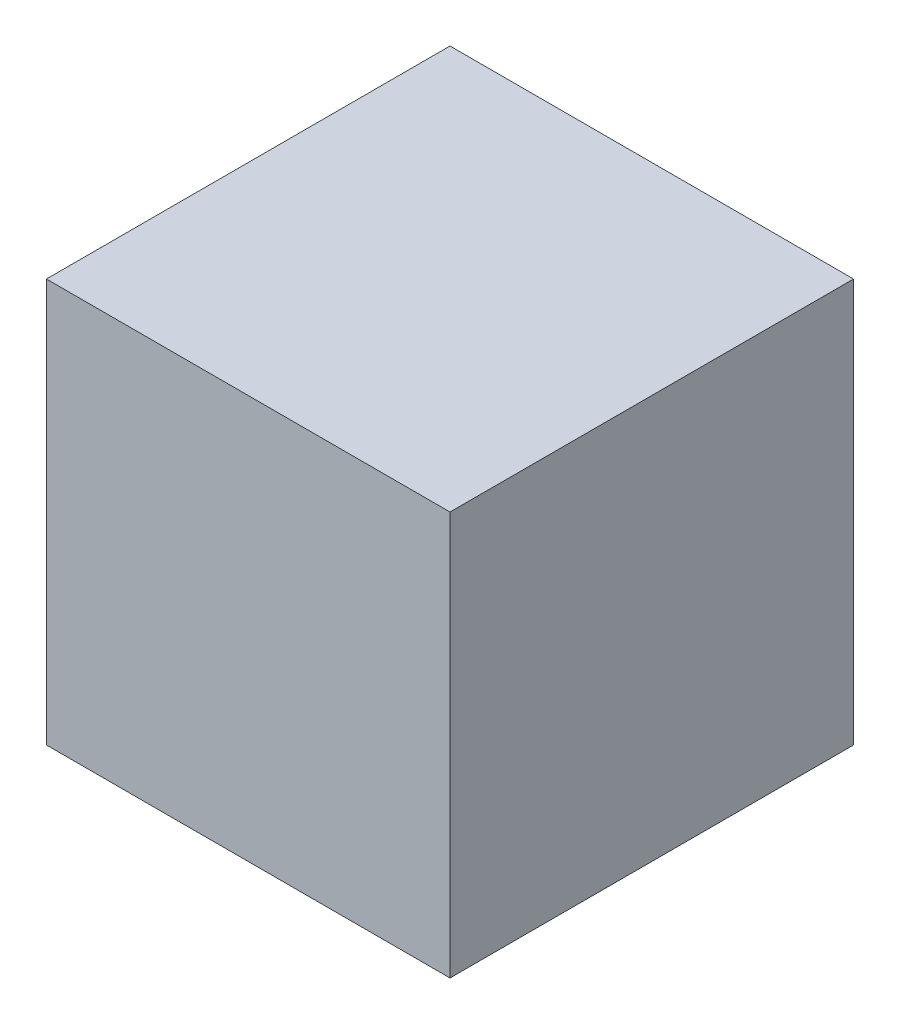
SolidWorks part; units mm, degrees
ref_plane "Plano frontal" through (0, 0, 0) normal (0, 0, 1) x (1, 0, 0)
ref_plane "Plano superior" through (0, 0, 0) normal (0, 1, 0) x (1, 0, 0)
ref_plane "Plano direito" through (0, 0, 0) normal (1, 0, 0) x (0, 0, -1)
sketch "Esboço1" plane through (0, 0, 0) normal (0, 1, 0) x (1, 0, 0)
  line L1 (5, -5) -> (-5, -5)
  line L2 (5, -5) -> (5, 5)
  line L3 (5, 5) -> (-5, 5)
  line L4 (-5, -5) -> (-5, 5)
  line L5 (5, -5) -> (-5, 5) construction
  line L6 (5, 5) -> (-5, -5) construction
  point P0 (0, 0)
  dimension "D1" = 10
  dimension "D2" = 10
extrude "Ressalto-extrusão1" add sketch "Esboço1" along normal mid plane 10
